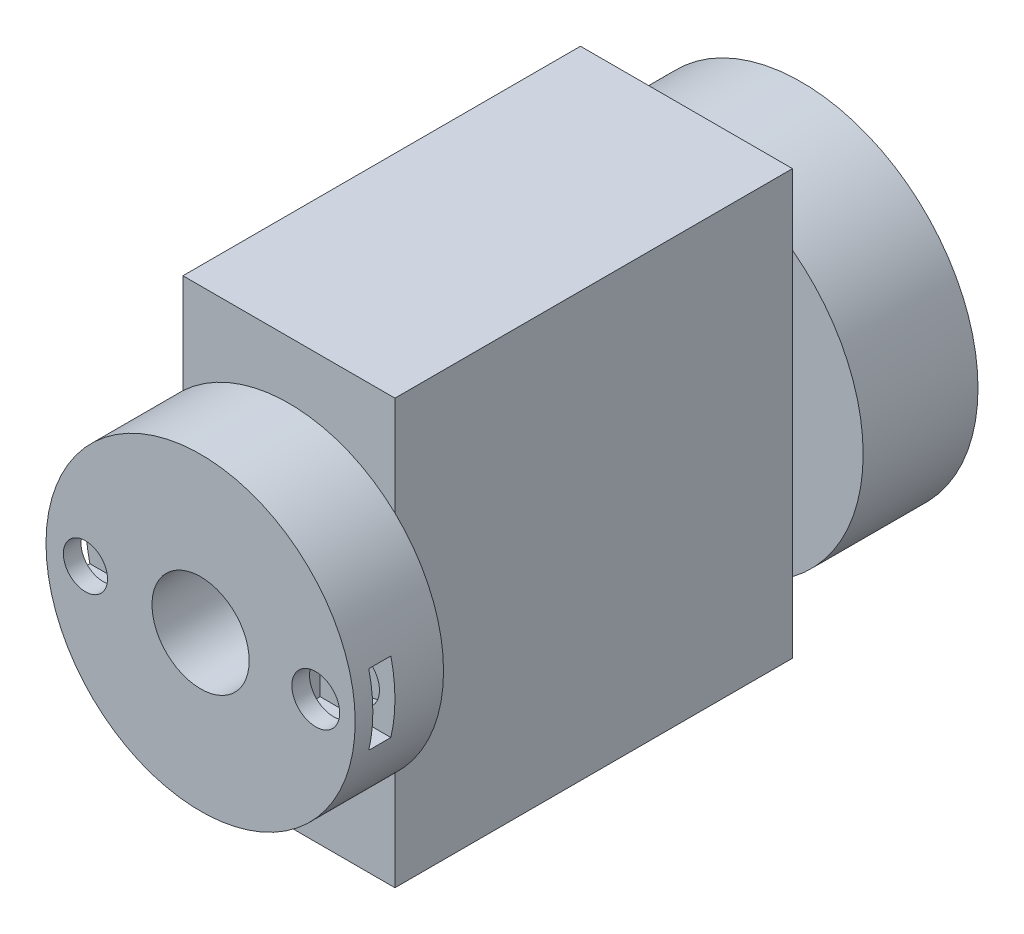
SolidWorks part; units mm, degrees
ref_plane "Plan de face" through (0, 0, 0) normal (0, 0, 1) x (1, 0, 0)
ref_plane "Plan de dessus" through (0, 0, 0) normal (0, 1, 0) x (1, 0, 0)
ref_plane "Plan de droite" through (0, 0, 0) normal (1, 0, 0) x (0, 0, -1)
sketch "Esquisse1" plane through (0, 0, 0) normal (0, 0, 1) x (1, 0, 0)
  circle A0 centre (0, 0) radius 17.5
  dimension "D1" = 35
extrude "Boss.-Extru.1" add sketch "Esquisse1" along normal blind 10
sketch "Esquisse3" plane through (0, 0, 10) normal (0, 0, 1) x (1, 0, 0)
  line L0 (0, 17.5) -> (0, -17.5) construction
  line L1 (-17.5, 0) -> (17.5, 0) construction
  line L2 (17.0367, -4) -> (9.0367, -4)
  line L3 (-17.0367, 4) -> (-9.0367, 4)
  line L4 (-17.0367, 4) -> (-17.0367, -4)
  line L5 (-17.0367, -4) -> (-9.0367, -4)
  line L6 (-9.0367, 4) -> (-9.0367, -4)
  line L7 (9.0367, 4) -> (9.0367, -4)
  line L8 (17.0367, 4) -> (9.0367, 4)
  line L9 (17.0367, 4) -> (17.0367, -4)
  circle A0 centre (0, 0) radius 17.5 construction
  dimension "D1" = 8
  dimension "D2" = 8
  dimension "D3" = 4
extrude "Boss.-Extru.3" add sketch "Esquisse3" along normal blind 4.5
sketch "Esquisse4" plane through (-17.0367, 0, 0) normal (-1, 0, 0) x (0, 0, 1)
  line L0 (14.5, 4) -> (14.5, -4) construction
  line L1 (14.5, -4) -> (0, -4) construction
  line L2 (0, 17.5) -> (0, -17.5) construction
  line L3 (0, -4) -> (0, 4) construction
  line L4 (0, 4) -> (14.5, 4) construction
  line L5 (10, 4) -> (10, -4) construction
  line L6 (8, 4) -> (5.5, 4)
  line L7 (8, 4) -> (8, -4)
  line L8 (8, -4) -> (5.5, -4)
  line L9 (5.5, 4) -> (5.5, -4)
  dimension "D1" = 2.5
  dimension "D2" = 2
extrude "Enlèv. mat.-Extru.1" cut sketch "Esquisse4" against normal blind 8 and the other way blind 1
sketch "Esquisse5" plane through (0, 0, 14.5) normal (0, 0, 1) x (1, 0, 0)
  line L0 (-9.0367, 4) -> (-17.0367, 4) construction
  line L1 (-9.0367, -4) -> (-9.0367, 4) construction
  circle A0 centre (-13.0367, 0) radius 2.5
  dimension "D1" = 5
  dimension "D2" = 4
  dimension "D3" = 4
extrude "Enlèv. mat.-Extru.2" cut sketch "Esquisse5" against normal blind 10.5
sketch "Esquisse6" plane through (0, 0, 14.5) normal (0, 0, 1) x (1, 0, 0)
  line L1 (-17.0367, 4) -> (-9.0367, 4)
  line L2 (-17.0367, 4) -> (-17.0367, -4)
  line L3 (-17.0367, -4) -> (-9.0367, -4)
  line L4 (-9.0367, 4) -> (-9.0367, -4)
  circle A0 centre (-13.0367, 0) radius 2.5
extrude "Enlèv. mat.-Extru.3" cut sketch "Esquisse6" against normal blind 4.5
sketch "Esquisse7" plane through (17.0367, 0, 0) normal (1, 0, 0) x (0, 0, -1)
  line L0 (-14.5, 4) -> (-14.5, -4) construction
  line L1 (-14.5, -4) -> (0, -4) construction
  line L2 (0, -17.5) -> (0, 17.5) construction
  line L3 (0, -4) -> (0, 4) construction
  line L4 (0, 4) -> (-14.5, 4) construction
  line L5 (-10, 4) -> (-10, -4) construction
  line L6 (-8, 4) -> (-5.5, 4)
  line L7 (-8, 4) -> (-8, -4)
  line L8 (-8, -4) -> (-5.5, -4)
  line L9 (-5.5, 4) -> (-5.5, -4)
  dimension "D1" = 2.5
  dimension "D2" = 2
extrude "Enlèv. mat.-Extru.4" cut sketch "Esquisse7" against normal blind 8 and the other way blind 1
sketch "Esquisse8" plane through (0, 0, 14.5) normal (0, 0, 1) x (1, 0, 0)
  line L0 (17.0367, 4) -> (9.0367, 4) construction
  line L1 (9.0367, 4) -> (9.0367, -4) construction
  circle A0 centre (13.0367, 0) radius 2.7075
  dimension "D1" = 4
  dimension "D2" = 4
extrude "Enlèv. mat.-Extru.5" cut sketch "Esquisse8" against normal blind 10.5
sketch "Esquisse9" plane through (0, 0, 14.5) normal (0, 0, 1) x (1, 0, 0)
  line L1 (9.0367, 4) -> (17.0367, 4)
  line L2 (9.0367, 4) -> (9.0367, -4)
  line L3 (9.0367, -4) -> (17.0367, -4)
  line L4 (17.0367, 4) -> (17.0367, -4)
  circle A0 centre (13.0367, 0) radius 2.7075
extrude "Enlèv. mat.-Extru.6" cut sketch "Esquisse9" against normal blind 4.5
sketch "Esquisse10" plane through (0, 0, 10) normal (0, 0, 1) x (1, 0, 0)
  circle A0 centre (0, 0) radius 5.5
  dimension "D1" = 11
extrude "Enlèv. mat.-Extru.7" cut sketch "Esquisse10" against normal through all
sketch "Esquisse11" plane through (0, 0, 0) normal (0, 0, -1) x (-1, 0, 0)
  line L1 (12, 24) -> (-12, 24)
  line L2 (12, 24) -> (12, -24)
  line L3 (12, -24) -> (-12, -24)
  line L4 (-12, 24) -> (-12, -24)
  line L5 (12, 24) -> (-12, -24) construction
  line L6 (12, -24) -> (-12, 24) construction
  point P0 (0, 0)
  dimension "D1" = 48
  dimension "D2" = 24
extrude "Boss.-Extru.4" add sketch "Esquisse11" along normal blind 45
sketch "Esquisse12" plane through (0, 0, -45) normal (0, 0, -1) x (-1, 0, 0)
  circle A0 centre (0, 0) radius 20
  dimension "D1" = 40
extrude "Boss.-Extru.5" add sketch "Esquisse12" along normal blind 13
sketch "Esquisse13" plane through (0, 0, -58) normal (0, 0, -1) x (-1, 0, 0)
  circle A0 centre (0, 0) radius 11.5
  dimension "D1" = 23
extrude "Enlèv. mat.-Extru.8" cut sketch "Esquisse13" against normal blind 8
